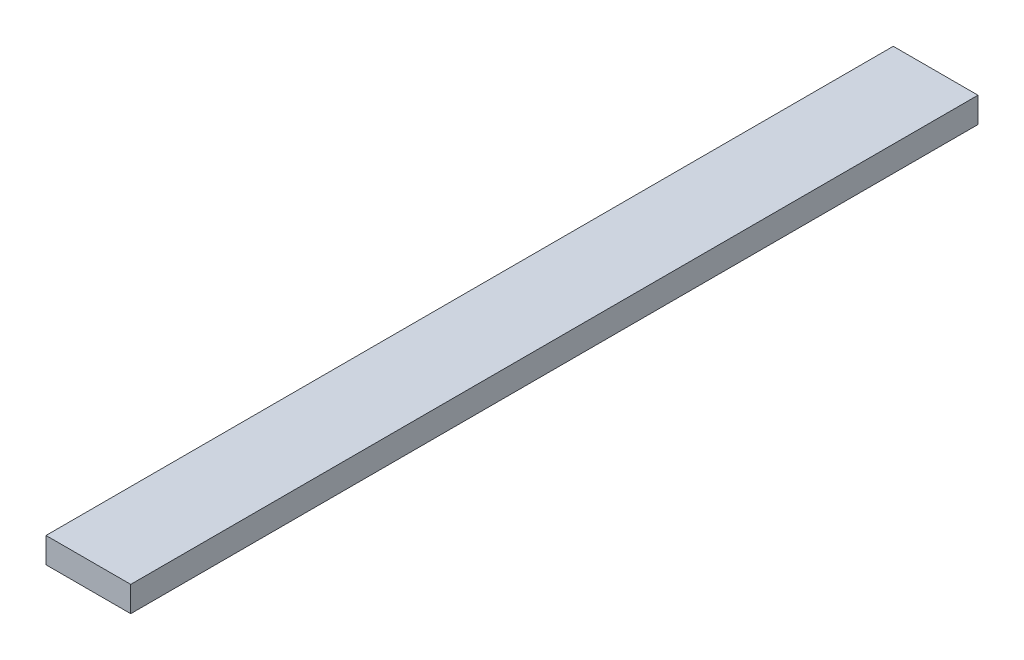
SolidWorks part; units mm, degrees
material "Balsa"
ref_plane "Alzado" through (0, 0, 0) normal (0, 0, 1) x (1, 0, 0)
ref_plane "Planta" through (0, 0, 0) normal (0, 1, 0) x (1, 0, 0)
ref_plane "Vista lateral" through (0, 0, 0) normal (1, 0, 0) x (0, 0, -1)
sketch "Croquis2" plane through (0, 0, 0) normal (1, 0, 0) x (0, 0, -1)
  line L1 (250, -7.5) -> (-250, -7.5)
  line L2 (250, -7.5) -> (250, 7.5)
  line L3 (250, 7.5) -> (-250, 7.5)
  line L4 (-250, -7.5) -> (-250, 7.5)
  line L5 (250, -7.5) -> (-250, 7.5) construction
  line L6 (250, 7.5) -> (-250, -7.5) construction
  point P0 (0, 0)
  dimension "D1" = 15
  dimension "D2" = 500
extrude "Saliente-Extruir1" add sketch "Croquis2" along normal blind 50
